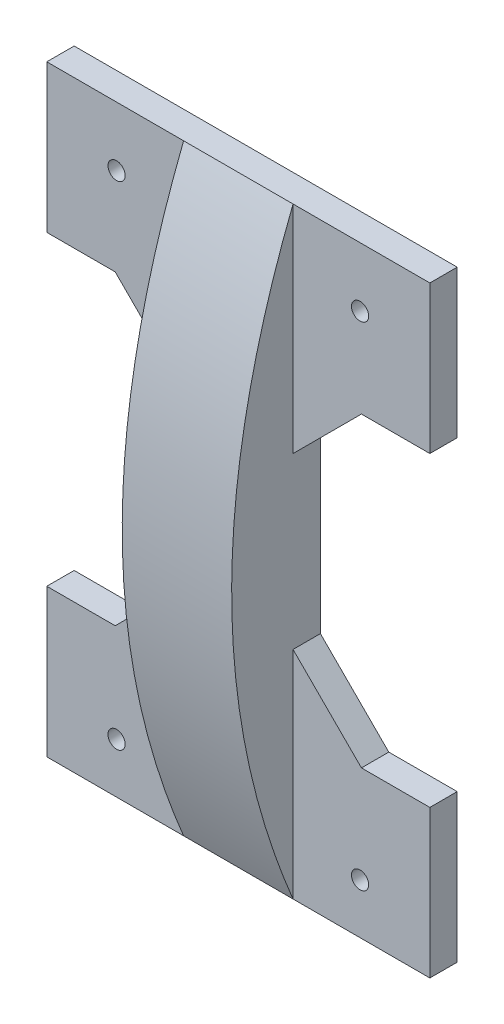
SolidWorks part; units mm, degrees
ref_plane "前视基准面" through (0, 0, 0) normal (0, 0, 1) x (1, 0, 0)
ref_plane "上视基准面" through (0, 0, 0) normal (0, 1, 0) x (1, 0, 0)
ref_plane "右视基准面" through (0, 0, 0) normal (1, 0, 0) x (0, 0, -1)
other "Configuration Table"
sketch "草图1" plane through (0, 0, 0) normal (0, 0, 1) x (1, 0, 0)
  line L1 (-42.6713, 44.6574) -> (27.3287, 44.6574)
  line L2 (-42.6713, 44.6574) -> (-42.6713, -65.3426)
  line L3 (-42.6713, -65.3426) -> (27.3287, -65.3426)
  line L4 (27.3287, 44.6574) -> (27.3287, -65.3426)
  dimension "D1" = 110
  dimension "D2" = 70
extrude "凸台-拉伸1" add sketch "草图1" along normal blind 5
sketch "草图2" plane through (0, 0, 5) normal (0, 0, 1) x (1, 0, 0)
  line L0 (-42.6713, 44.6574) -> (-42.6713, -65.3426) construction
  line L1 (-42.6713, -56.1888) -> (27.3287, -56.1888) construction
  line L2 (27.3287, -65.3426) -> (27.3287, 44.6574) construction
  line L3 (-42.6713, 33.8112) -> (27.3287, 33.8112) construction
  line L4 (-29.9213, 33.8112) -> (-29.9213, -56.1888) construction
  line L5 (14.5787, 33.8112) -> (14.5787, -56.1888) construction
  circle A0 centre (-29.9213, 33.8112) radius 1.57
  circle A1 centre (14.5787, 33.8112) radius 1.57
  circle A2 centre (-29.9213, -56.1888) radius 1.57
  circle A3 centre (14.5787, -56.1888) radius 1.57
  point P12 (-7.6713, 33.8112)
  dimension "D2" = 22.25
  dimension "D1" = 90
  dimension "D3" = 22.25
extrude "切除-拉伸1" cut sketch "草图2" against normal blind 5
sketch "草图3" plane through (0, 0, 5) normal (0, 0, 1) x (1, 0, 0)
  line L0 (-42.6713, 44.6574) -> (-42.6713, -65.3426) construction
  line L1 (-42.6713, 17.6574) -> (-30.1713, 17.6574)
  line L2 (-42.6713, 17.6574) -> (-42.6713, -38.3426)
  line L3 (-42.6713, -38.3426) -> (-30.1713, -38.3426)
  line L4 (-17.6713, 5.1574) -> (-17.6713, -25.8426)
  line L5 (14.8287, 17.6574) -> (27.3287, 17.6574)
  line L6 (2.3287, 5.1574) -> (2.3287, -25.8426)
  line L7 (14.8287, -38.3426) -> (27.3287, -38.3426)
  line L8 (27.3287, 17.6574) -> (27.3287, -38.3426)
  line L9 (27.3287, 44.6574) -> (-42.6713, 44.6574) construction
  line L10 (-42.6713, -65.3426) -> (27.3287, -65.3426) construction
  line L11 (27.3287, -65.3426) -> (27.3287, 44.6574) construction
  line L12 (-30.1713, 17.6574) -> (-17.6713, 5.1574)
  line L13 (-30.1713, -38.3426) -> (-17.6713, -25.8426)
  line L14 (14.8287, 17.6574) -> (2.3287, 5.1574)
  line L15 (14.8287, -38.3426) -> (2.3287, -25.8426)
  dimension "D1" = 27
  dimension "D2" = 27
  dimension "D3" = 0
  dimension "D4" = 27
  dimension "D5" = 27
  dimension "D8" = 45
  dimension "D9" = 45
  dimension "D10" = 45
  dimension "D11" = 45
extrude "切除-拉伸2" cut sketch "草图3" against normal blind 5
sketch "草图4" plane through (0, 0, 5) normal (0, 0, 1) x (1, 0, 0)
  line L0 (-7.6713, 44.6574) -> (-7.6713, -65.3426) construction
  line L1 (27.3287, 44.6574) -> (-42.6713, 44.6574) construction
  line L2 (-42.6713, -65.3426) -> (27.3287, -65.3426) construction
  line L4 (-12.2339, 44.6574) -> (-3.1087, 44.6574)
  line L5 (-12.2339, 44.6574) -> (-12.2339, -65.3426)
  line L6 (-12.2339, -65.3426) -> (-3.1087, -65.3426)
  line L7 (-3.1087, 44.6574) -> (-3.1087, -65.3426)
  line L8 (-12.2339, 44.6574) -> (-3.1087, -65.3426) construction
  line L9 (-12.2339, -65.3426) -> (-3.1087, 44.6574) construction
  point P6 (-7.6713, -10.3426)
  point P11 (0, 0)
sketch "草图6" plane through (2.3287, 0, 0) normal (1, 0, 0) x (0, 0, -1)
  line L1 (-5, -65.3426) -> (0, -65.3426) construction
  line L8 (-5, 44.6574) -> (-5, -65.3426)
  spline S0 degree 2 poles (-5, 44.6574) (-27.4317, -11.8555) (-5, -65.3426) knots 0 0 0 1 1 1
  point P7 (-2.5, -65.3426)
extrude "凸台-拉伸3" add sketch "草图6" against normal up to vertex
